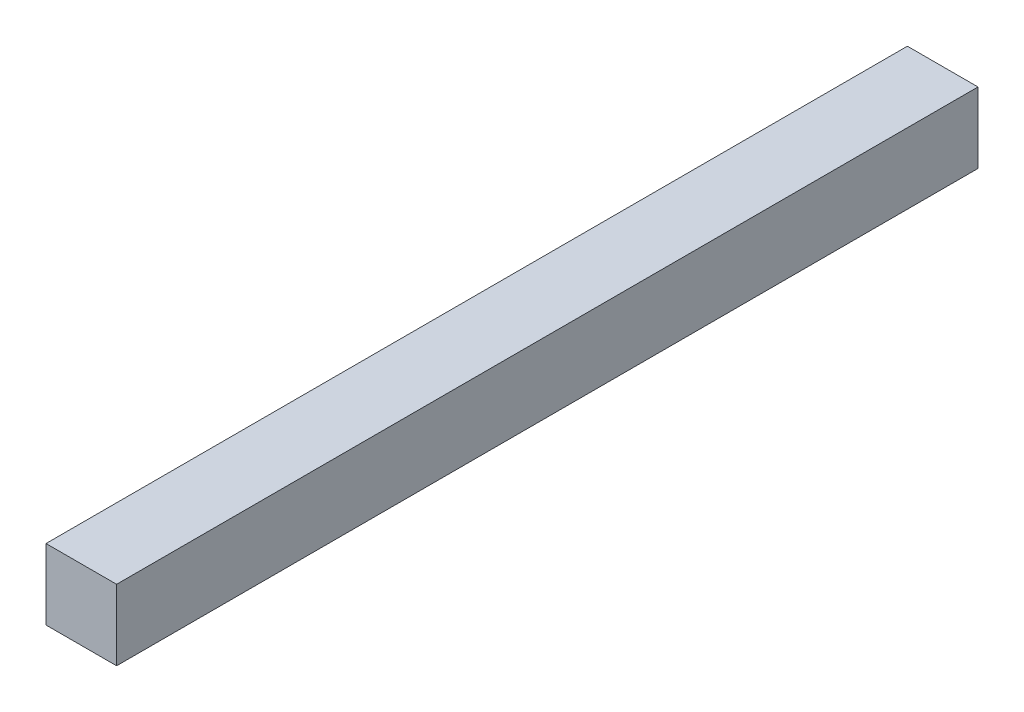
SolidWorks part; units mm, degrees
ref_plane "Front" through (0, 0, 0) normal (0, 0, 1) x (1, 0, 0)
ref_plane "Top" through (0, 0, 0) normal (0, 1, 0) x (1, 0, 0)
ref_plane "Right" through (0, 0, 0) normal (1, 0, 0) x (0, 0, -1)
sketch "草图1" plane through (0, 0, 0) normal (0, 0, 1) x (1, 0, 0)
  line L1 (-5, 5) -> (5, 5)
  line L2 (-5, 5) -> (-5, -5)
  line L3 (-5, -5) -> (5, -5)
  line L4 (5, 5) -> (5, -5)
  dimension "D1" = 10
  dimension "D2" = 10
  dimension "D3" = 5
  dimension "D4" = 5
extrude "凸台-拉伸1" add sketch "草图1" along normal blind 122
sketch "草图2" plane through (0, 0, 0) normal (0, 0, -1) x (-1, 0, 0)
  circle A0 centre (0, 0) radius 4
extrude "切除-拉伸1" cut sketch "草图2" against normal blind 120
sketch "草图3" plane through (0, -5, 0) normal (0, -1, 0) x (1, 0, 0)
  circle A0 centre (0, 6.2314) radius 2
extrude "切除-拉伸2" cut sketch "草图3" against normal blind 2
